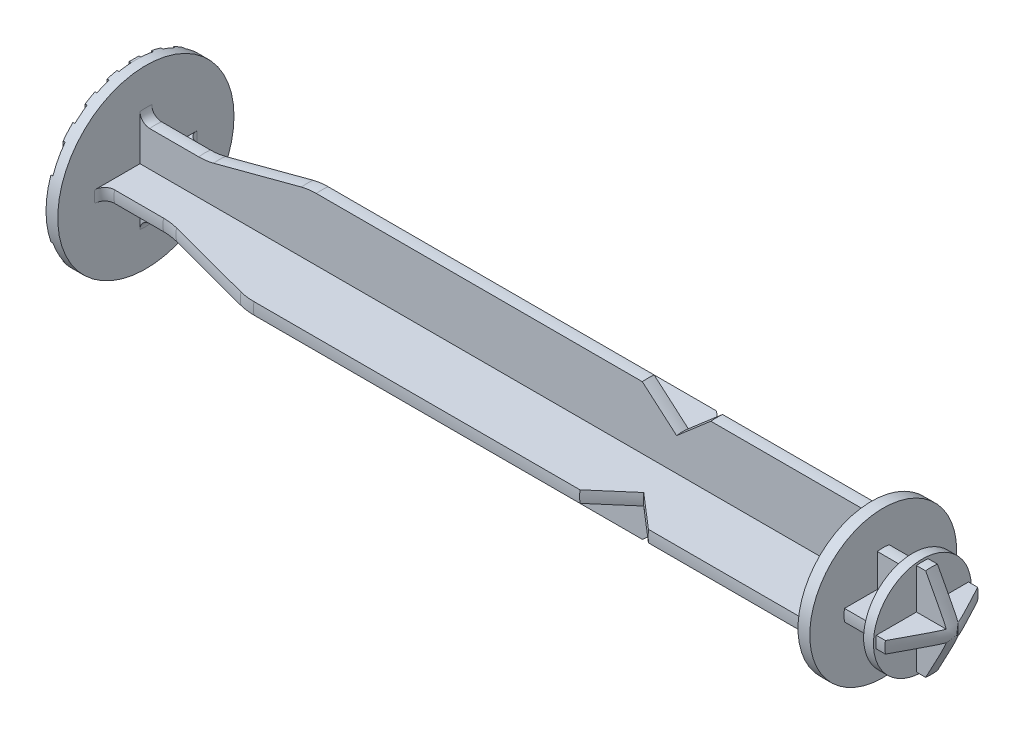
SolidWorks part; units mm, degrees
material "Polyethylene Cross-Linked"
ref_plane "Front Plane" through (0, 0, 0) normal (0, 0, 1) x (1, 0, 0)
ref_plane "Top Plane" through (0, 0, 0) normal (0, 1, 0) x (1, 0, 0)
ref_plane "Right Plane" through (0, 0, 0) normal (1, 0, 0) x (0, 0, -1)
sketch "Sketch1" plane through (0, 0, 0) normal (0, 0, 1) x (1, 0, 0)
  line L0 (84, 0) -> (-84, 0) construction
  line L1 (0, 0) -> (0, 9)
  line L2 (0, 9) -> (1.2, 9)
  line L3 (1.2, 9) -> (1.2, 5.25)
  line L4 (2.2, 4.25) -> (7.2, 4.25)
  line L5 (8.7274, 4.4477) -> (17.6726, 6.8023)
  line L6 (19.2, 7) -> (52.5, 7)
  line L7 (52.5, 7) -> (56, 4)
  line L8 (56, 4) -> (59.5, 7)
  line L9 (59.5, 7) -> (75.3, 7)
  line L10 (75.3, 7) -> (75.3, 7.5)
  line L11 (75.3, 7.5) -> (76.5, 7.5)
  line L12 (76.5, 7.5) -> (76.5, 4)
  line L13 (76.5, 4) -> (79.5, 4)
  line L14 (79.5, 4) -> (79.5, 5)
  line L15 (79.5, 5) -> (81.3, 5)
  line L16 (81.3, 5) -> (84, 0)
  line L17 (0, 0) -> (84, 0)
  arc A0 (1.2, 5.25) -> (2.2, 4.25) centre (2.2, 5.25) ccw
  arc A1 (17.6726, 6.8023) -> (19.2, 7) centre (19.2, 1) cw
  arc A2 (7.2, 4.25) -> (8.7274, 4.4477) centre (7.2, 10.25) ccw
  point P4 (0, 0)
  dimension "D14" = 1
  dimension "D15" = 6
  dimension "D1" = 1.2
  dimension "D2" = 7.5
  dimension "D3" = 18
  dimension "D4" = 8.5
  dimension "D5" = 84
  dimension "D6" = 8
  dimension "D7" = 7
  dimension "D8" = 14
  dimension "D9" = 15
  dimension "D10" = 8
  dimension "D11" = 10
  dimension "D12" = 28
  dimension "D13" = 4.5
  dimension "D16" = 6
  dimension "D17" = 18
  dimension "D18" = 2.7
  dimension "D19" = 118.369
revolve "Revolve1" add sketch "Sketch1" angle 360 about L0
sketch "Sketch2" plane through (1.2, 0, 0) normal (1, 0, 0) x (0, 0, -1)
  line L0 (17.7295, 0) -> (-17.7295, 0) construction
  line L1 (0, -17.5817) -> (0, 17.5817) construction
  line L2 (-0.6, 8.98) -> (-0.6, 0.6)
  line L3 (-0.6, 0.6) -> (-8.98, 0.6)
  line L4 (0.6, 0.6) -> (0.6, 8.98)
  line L5 (8.98, 0.6) -> (0.6, 0.6)
  line L6 (0.6, -0.6) -> (8.98, -0.6)
  line L7 (0.6, -8.98) -> (0.6, -0.6)
  line L8 (-0.6, -0.6) -> (-0.6, -8.98)
  line L9 (-8.98, -0.6) -> (-0.6, -0.6)
  circle A0 centre (0, 0) radius 9 construction
  arc A1 (-8.98, 0.6) -> (-8.98, -0.6) centre (0, 0) ccw
  arc A2 (0.6, 8.98) -> (-0.6, 8.98) centre (0, 0) ccw
  arc A3 (8.98, -0.6) -> (8.98, 0.6) centre (0, 0) ccw
  arc A4 (-0.6, -8.98) -> (0.6, -8.98) centre (0, 0) ccw
  point P5 (0, 0)
  point P9 (0, 0)
  point P27 (0, 0)
  dimension "D3" = 1.2
  dimension "D2" = 4
extrude "Cut-Extrude1" cut sketch "Sketch2" along normal up to surface (74.1 mm away) flip side to cut up to face at (75.3, 0, -7)
sketch "Sketch3" plane through (0, 0, 0) normal (-1, 0, 0) x (0, 0, 1)
  line L0 (2.75, -8.9861) -> (1.75, -8.9861)
  line L1 (0.5, -8.9861) -> (-0.5, -8.9861)
  line L2 (0.5, -8.9861) -> (0.5, 8.9861)
  line L3 (0.5, 8.9861) -> (-0.5, 8.9861)
  line L4 (-0.5, -8.9861) -> (-0.5, 8.9861)
  line L5 (0.5, -8.9861) -> (-0.5, 8.9861) construction
  line L6 (0.5, 8.9861) -> (-0.5, -8.9861) construction
  line L7 (1.75, -8.9861) -> (1.75, 8.9861)
  line L8 (2.75, 8.9861) -> (1.75, 8.9861)
  line L9 (2.75, -8.9861) -> (2.75, 8.9861)
  line L10 (5, -8.9861) -> (4, -8.9861)
  line L11 (4, -8.9861) -> (4, 8.9861)
  line L12 (5, 8.9861) -> (4, 8.9861)
  line L13 (5, -8.9861) -> (5, 8.9861)
  line L14 (7.25, -8.9861) -> (6.25, -8.9861)
  line L15 (6.25, -8.9861) -> (6.25, 8.9861)
  line L16 (7.25, 8.9861) -> (6.25, 8.9861)
  line L17 (7.25, -8.9861) -> (7.25, 8.9861)
  line L18 (9.5, -8.9861) -> (8.5, -8.9861)
  line L19 (8.5, -8.9861) -> (8.5, 8.9861)
  line L20 (9.5, 8.9861) -> (8.5, 8.9861)
  line L21 (9.5, -8.9861) -> (9.5, 8.9861)
  line L22 (11.75, -8.9861) -> (10.75, -8.9861)
  line L23 (10.75, -8.9861) -> (10.75, 8.9861)
  line L24 (11.75, 8.9861) -> (10.75, 8.9861)
  line L25 (11.75, -8.9861) -> (11.75, 8.9861)
  line L26 (14, -8.9861) -> (13, -8.9861)
  line L27 (13, -8.9861) -> (13, 8.9861)
  line L28 (14, 8.9861) -> (13, 8.9861)
  line L29 (14, -8.9861) -> (14, 8.9861)
  line L30 (-1.75, -8.9861) -> (-2.75, -8.9861)
  line L31 (-2.75, -8.9861) -> (-2.75, 8.9861)
  line L32 (-1.75, 8.9861) -> (-2.75, 8.9861)
  line L33 (-1.75, -8.9861) -> (-1.75, 8.9861)
  line L34 (-4, -8.9861) -> (-5, -8.9861)
  line L35 (-5, -8.9861) -> (-5, 8.9861)
  line L36 (-4, 8.9861) -> (-5, 8.9861)
  line L37 (-4, -8.9861) -> (-4, 8.9861)
  line L38 (-6.25, -8.9861) -> (-7.25, -8.9861)
  line L39 (-7.25, -8.9861) -> (-7.25, 8.9861)
  line L40 (-6.25, 8.9861) -> (-7.25, 8.9861)
  line L41 (-6.25, -8.9861) -> (-6.25, 8.9861)
  line L42 (-8.5, -8.9861) -> (-9.5, -8.9861)
  line L43 (-9.5, -8.9861) -> (-9.5, 8.9861)
  line L44 (-8.5, 8.9861) -> (-9.5, 8.9861)
  line L45 (-8.5, -8.9861) -> (-8.5, 8.9861)
  line L46 (-10.75, -8.9861) -> (-11.75, -8.9861)
  line L47 (-11.75, -8.9861) -> (-11.75, 8.9861)
  line L48 (-10.75, 8.9861) -> (-11.75, 8.9861)
  line L49 (-10.75, -8.9861) -> (-10.75, 8.9861)
  line L50 (-13, -8.9861) -> (-14, -8.9861)
  line L51 (-14, -8.9861) -> (-14, 8.9861)
  line L52 (-13, 8.9861) -> (-14, 8.9861)
  line L53 (-13, -8.9861) -> (-13, 8.9861)
  circle A0 centre (0, 0) radius 9 construction
  point P0 (0, 0)
  dimension "D1" = 1
  dimension "D3" = 2.25
  dimension "D2" = 7
  dimension "D4" = 7
extrude "Cut-Extrude2" cut sketch "Sketch3" against normal blind 0.2 flip side to cut
sketch "Sketch4" plane through (76.5, 0, 0) normal (1, 0, 0) x (0, 0, -1)
  line L8 (0.6, 0.6) -> (0.6, 8.98)
  line L9 (-0.6, 8.98) -> (-0.6, 0.6)
  line L10 (-0.6, 0.6) -> (-8.98, 0.6)
  line L11 (-8.98, -0.6) -> (-0.6, -0.6)
  line L12 (-0.6, -0.6) -> (-0.6, -8.98)
  line L13 (0.6, -8.98) -> (0.6, -0.6)
  line L14 (0.6, -0.6) -> (8.98, -0.6)
  line L15 (8.98, 0.6) -> (0.6, 0.6)
  line L16 (0.6, 0.6) -> (0.6, 8.98)
  line L17 (-0.6, 8.98) -> (-0.6, 0.6)
  line L18 (-0.6, 0.6) -> (-8.98, 0.6)
  line L19 (-8.98, -0.6) -> (-0.6, -0.6)
  line L20 (-0.6, -0.6) -> (-0.6, -8.98)
  line L21 (0.6, -8.98) -> (0.6, -0.6)
  line L22 (0.6, -0.6) -> (8.98, -0.6)
  line L23 (8.98, 0.6) -> (0.6, 0.6)
  arc A4 (0.6, 8.98) -> (-0.6, 8.98) centre (0, 0) ccw
  arc A5 (-8.98, 0.6) -> (-8.98, -0.6) centre (0, 0) ccw
  arc A6 (-0.6, -8.98) -> (0.6, -8.98) centre (0, 0) ccw
  arc A7 (8.98, -0.6) -> (8.98, 0.6) centre (0, 0) ccw
  arc A8 (0.6, 8.98) -> (-0.6, 8.98) centre (0, 0) ccw
  arc A9 (-8.98, 0.6) -> (-8.98, -0.6) centre (0, 0) ccw
  arc A10 (-0.6, -8.98) -> (0.6, -8.98) centre (0, 0) ccw
  arc A11 (8.98, -0.6) -> (8.98, 0.6) centre (0, 0) ccw
  dimension "D1" = 0
extrude "Cut-Extrude3" cut sketch "Sketch4" along normal up to surface (3 mm away) flip side to cut up to face at (79.5, 0, -4)
ref_plane "Plane1" through (84, 0, 0) normal (1, 0, 0) x (0, 0, -1)
sketch "Sketch5" plane through (84, 0, 0) normal (1, 0, 0) x (0, 0, -1)
  line L8 (0.6, 0.6) -> (0.6, 8.98)
  line L9 (-0.6, 8.98) -> (-0.6, 0.6)
  line L10 (-0.6, 0.6) -> (-8.98, 0.6)
  line L11 (-8.98, -0.6) -> (-0.6, -0.6)
  line L12 (-0.6, -0.6) -> (-0.6, -8.98)
  line L13 (0.6, -8.98) -> (0.6, -0.6)
  line L14 (0.6, -0.6) -> (8.98, -0.6)
  line L15 (8.98, 0.6) -> (0.6, 0.6)
  line L16 (0.6, 0.6) -> (0.6, 4.712)
  line L17 (-0.6, 4.712) -> (-0.6, 0.6)
  line L18 (-0.6, 0.6) -> (-4.712, 0.6)
  line L19 (-4.712, -0.6) -> (-0.6, -0.6)
  line L20 (-0.6, -0.6) -> (-0.6, -4.712)
  line L21 (0.6, -4.712) -> (0.6, -0.6)
  line L22 (0.6, -0.6) -> (4.712, -0.6)
  line L23 (4.712, 0.6) -> (0.6, 0.6)
  arc A0 (-4.712, 0.6) -> (-4.712, -0.6) centre (0, 0) ccw
  arc A1 (4.712, -0.6) -> (4.712, 0.6) centre (0, 0) ccw
  arc A2 (0.6, 4.712) -> (-0.6, 4.712) centre (0, 0) ccw
  arc A3 (-0.6, -4.712) -> (0.6, -4.712) centre (0, 0) ccw
  arc A4 (0.6, 8.98) -> (-0.6, 8.98) centre (0, 0) ccw
  arc A5 (-8.98, 0.6) -> (-8.98, -0.6) centre (0, 0) ccw
  arc A6 (-0.6, -8.98) -> (0.6, -8.98) centre (0, 0) ccw
  arc A7 (8.98, -0.6) -> (8.98, 0.6) centre (0, 0) ccw
  dimension "D2" = 9.5
  dimension "D1" = 0
extrude "Cut-Extrude4" cut sketch "Sketch5" against normal blind 3.5 flip side to cut
